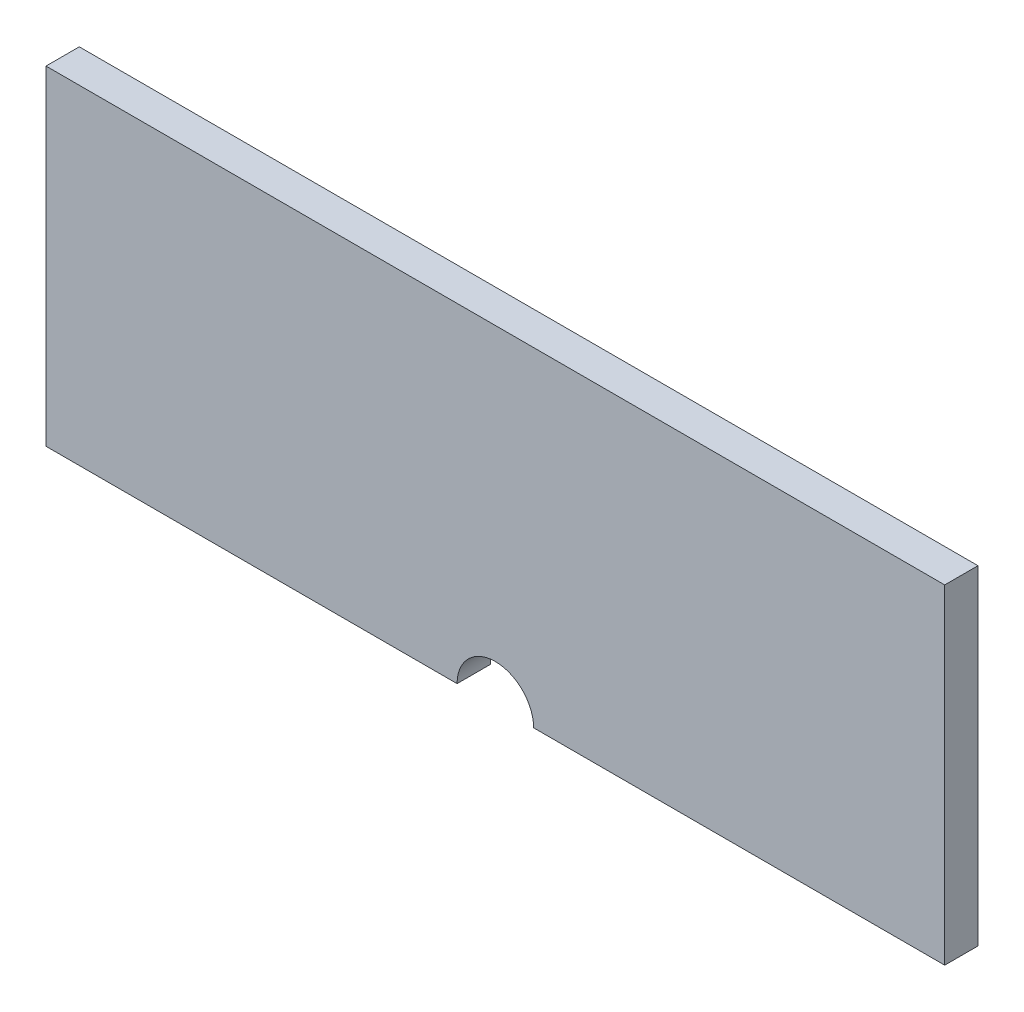
SolidWorks part; units mm, degrees
ref_plane "Front Plane" through (0, 0, 0) normal (0, 0, 1) x (1, 0, 0)
ref_plane "Top Plane" through (0, 0, 0) normal (0, 1, 0) x (1, 0, 0)
ref_plane "Right Plane" through (0, 0, 0) normal (1, 0, 0) x (0, 0, -1)
sketch "Sketch1" plane through (0, 0, 0) normal (0, 0, 1) x (1, 0, 0)
  line L0 (-11.5, -54.47) -> (-135, -54.47)
  line L1 (135, 44.47) -> (-135, 44.47)
  line L2 (135, 44.47) -> (135, -54.47)
  line L3 (135, -54.47) -> (11.5, -54.47)
  line L4 (-135, 44.47) -> (-135, -54.47)
  arc A0 (11.5, -54.47) -> (-11.5, -54.47) centre (0, -54.47) ccw
  point P0 (0, 0)
  point P7 (0, 0)
  dimension "D3" = 23
  dimension "D1" = 54.47
  dimension "D2" = 270
  dimension "D4" = 98.94
extrude "Boss-Extrude1" add sketch "Sketch1" along normal mid plane 10
